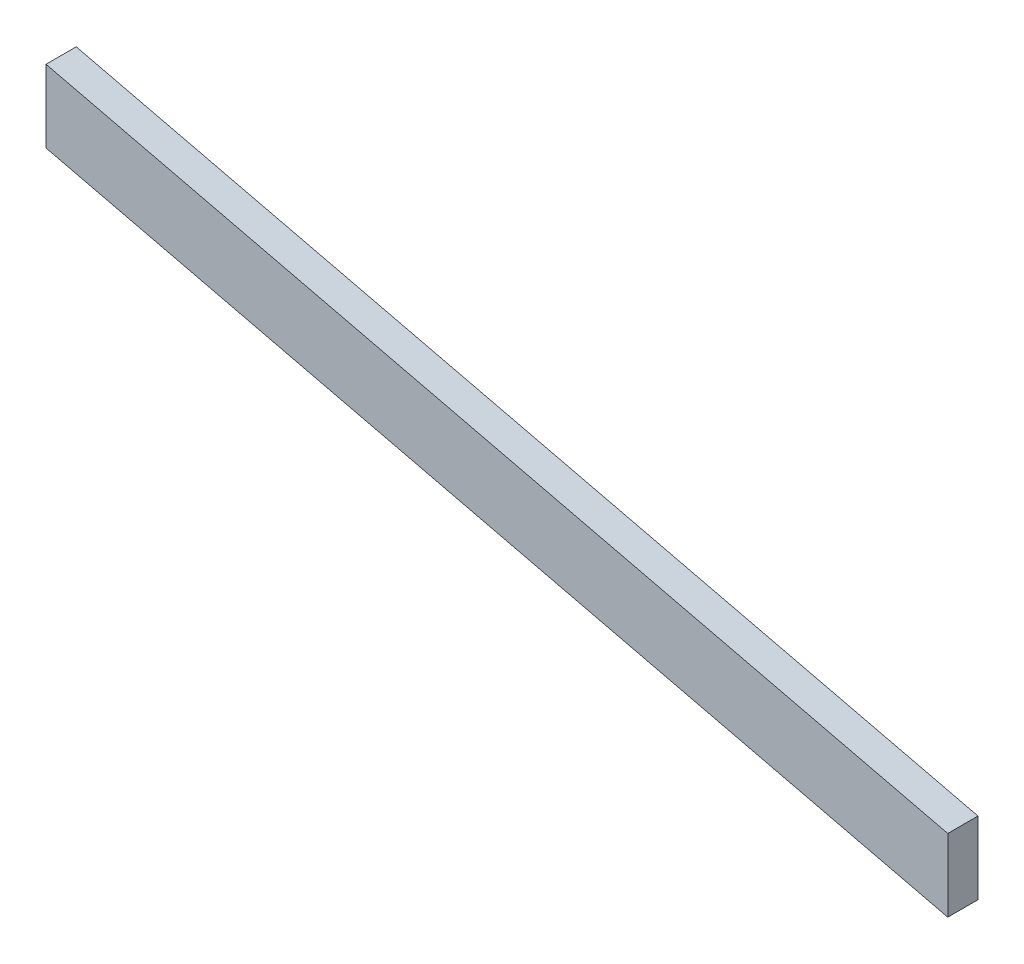
SolidWorks part; units mm, degrees
material "Pine"
ref_plane "Front Plane" through (0, 0, 0) normal (0, 0, 1) x (1, 0, 0)
ref_plane "Top Plane" through (0, 0, 0) normal (0, 1, 0) x (1, 0, 0)
ref_plane "Right Plane" through (0, 0, 0) normal (1, 0, 0) x (0, 0, -1)
sketch "Sketch1" plane through (0, 0, 0) normal (0, 0, 1) x (1, 0, 0)
  line L4 (-190.7934, 158.1241) -> (-190.7934, -204.6196) construction
  line L5 (-190.7934, -204.6196) -> (945.8566, -204.6196) construction
  line L15 (945.8566, -204.6196) -> (945.8566, 228.1963) construction
  line L16 (-190.7934, 158.1241) -> (945.8566, -113.2216)
  line L17 (945.8566, -113.2216) -> (945.8566, -204.6196)
  line L18 (945.8566, -204.6196) -> (-190.7934, 66.7261)
  line L19 (-190.7934, 66.7261) -> (-190.7934, 158.1241)
  dimension "D1" = 88.9
  dimension "D2" = 362.7437
  dimension "D4" = 1136.65
  dimension "D5" = 90
extrude "Boss-Extrude1" add sketch "Sketch1" along normal blind 38.1
